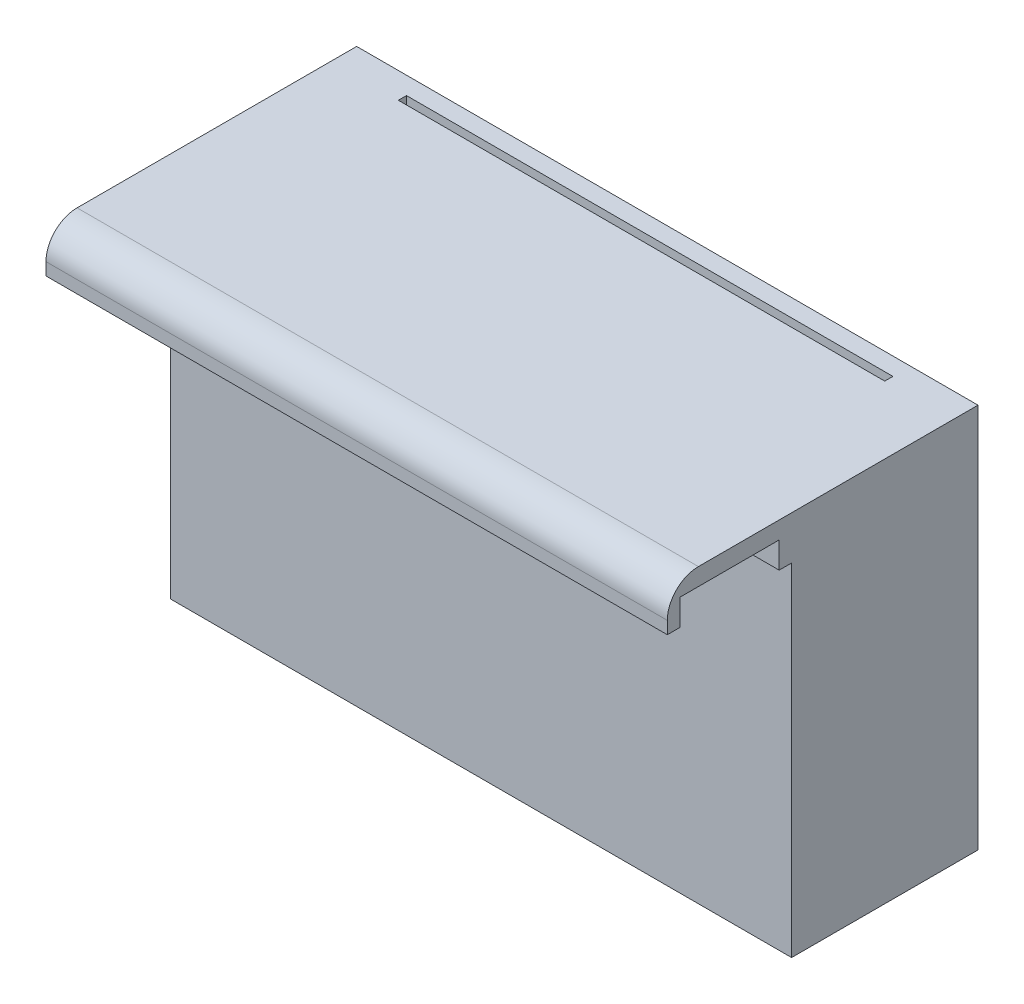
SolidWorks part; units mm, degrees
ref_plane "Front Plane" through (0, 0, 0) normal (0, 0, 1) x (1, 0, 0)
ref_plane "Top Plane" through (0, 0, 0) normal (0, 1, 0) x (1, 0, 0)
ref_plane "Right Plane" through (0, 0, 0) normal (1, 0, 0) x (0, 0, -1)
sketch "Sketch1" plane through (0, 0, 0) normal (0, 1, 0) x (1, 0, 0)
  line L1 (0, 0) -> (-100, 0)
  line L2 (0, 0) -> (0, 20)
  line L3 (0, 20) -> (-100, 20)
  line L4 (-100, 0) -> (-100, 20)
  dimension "D1" = 20
  dimension "D2" = 100
extrude "Boss-Extrude1" add sketch "Sketch1" along normal blind 7
sketch "Sketch2" plane through (-100, 0, 0) normal (-1, 0, 0) x (0, 0, 1)
  line L5 (-20, 0) -> (0, 0) construction
  line L6 (-2, -4.2141) -> (-18, -4.2141)
  line L7 (-2, -4.2141) -> (-2, 4.2141)
  line L8 (-2, 4.2141) -> (-18, 4.2141)
  line L9 (-18, -4.2141) -> (-18, 4.2141)
  line L10 (-2, -4.2141) -> (-18, 4.2141) construction
  line L11 (-2, 4.2141) -> (-18, -4.2141) construction
  point P0 (-10, 0)
  dimension "D1" = 16
extrude "Cut-Extrude1" cut sketch "Sketch2" against normal through all
sketch "Sketch3" plane through (0, 0, -20) normal (0, 0, -1) x (-1, 0, 0)
  line L0 (100, 7) -> (100, 0) construction
  line L1 (0, 7) -> (100, 7)
  line L2 (0, 7) -> (0, -55)
  line L3 (0, -55) -> (100, -55)
  line L4 (100, 7) -> (100, -55)
  dimension "D1" = 62
extrude "Boss-Extrude2" add sketch "Sketch3" along normal blind 30
sketch "Sketch4" plane through (0, 0, -50) normal (0, 0, -1) x (-1, 0, 0)
  line L0 (0, -24) -> (100, -24) construction
  line L1 (0, 7) -> (0, -55) construction
  line L2 (100, -55) -> (100, 7) construction
  line L3 (50, 7) -> (50, -24) construction
  line L4 (100, 7) -> (0, 7) construction
  line L6 (6, -52.25) -> (94, -52.25)
  line L7 (6, -52.25) -> (6, 4.25)
  line L8 (6, 4.25) -> (94, 4.25)
  line L9 (94, -52.25) -> (94, 4.25)
  line L10 (6, -52.25) -> (94, 4.25) construction
  line L11 (6, 4.25) -> (94, -52.25) construction
  dimension "D1" = 88
  dimension "D2" = 56.5
extrude "Cut-Extrude2" cut sketch "Sketch4" against normal blind 27.5
sketch "Sketch5" plane through (-94, 0, 0) normal (1, 0, 0) x (0, 0, -1)
  line L1 (22.5, -27.6063) -> (31.2, -27.6063) construction
  line L2 (22.5, -52.25) -> (22.5, 4.25) construction
  line L3 (38.8863, 2.25) -> (38.8863, 4.25) construction
  line L6 (31.2, 2.25) -> (38.8863, 2.25)
  line L10 (31.2, -50.25) -> (38.8863, -50.25)
  line L12 (22.5, 4.25) -> (50, 4.25) construction
  line L13 (38.8863, -50.25) -> (38.8863, -52.25) construction
  line L14 (22.5, -52.25) -> (50, -52.25) construction
  line L15 (31.2, 2.25) -> (31.2, -50.25)
  line L16 (38.8863, 2.25) -> (38.8863, -50.25)
  dimension "D1" = 8.7
  dimension "D2" = 52.5
extrude "Cut-Extrude3" cut sketch "Sketch5" against normal through all
sketch "Sketch6" plane through (-6, 0, 0) normal (-1, 0, 0) x (0, 0, 1)
  line L0 (-22.5, -24) -> (-50, -24) construction
  line L1 (-22.5, 4.25) -> (-22.5, -52.25) construction
  line L2 (-50, 4.25) -> (-50, -52.25) construction
  line L4 (-50, -17.5) -> (-22.5, -17.5)
  line L5 (-50, -17.5) -> (-50, -30.5)
  line L6 (-50, -30.5) -> (-22.5, -30.5)
  line L7 (-22.5, -17.5) -> (-22.5, -30.5)
  line L8 (-50, -17.5) -> (-22.5, -30.5) construction
  line L9 (-50, -30.5) -> (-22.5, -17.5) construction
  point P6 (-36.25, -24)
  point P11 (-44.5908, -17.5)
  point P12 (-22.5, -17.5)
  dimension "D1" = 13
extrude "Cut-Extrude4" cut sketch "Sketch6" against normal blind 3
sketch "Sketch7" plane through (0, 0, -50) normal (0, 0, -1) x (-1, 0, 0)
  line L0 (6, -52.25) -> (11, -52.25) construction
  line L1 (6, -52.25) -> (94, -52.25) construction
  line L2 (6, -52.25) -> (64, -52.25) construction
  line L3 (6, -52.25) -> (94, -52.25) construction
  line L5 (6, -52.25) -> (64, -52.25)
  line L6 (6, -52.25) -> (6, -54.55)
  line L7 (6, -54.55) -> (64, -54.55)
  line L8 (64, -52.25) -> (64, -54.55)
  dimension "D1" = 5
  dimension "D2" = 58
  dimension "D3" = 2.3
extrude "Cut-Extrude5" cut sketch "Sketch7" against normal blind 23
sketch "Sketch9" plane through (0, -52.25, 0) normal (0, 1, 0) x (1, 0, 0)
  line L0 (-37.9606, 22.5) -> (-37.9606, 38.5) construction
  line L1 (-6, 22.5) -> (-94, 22.5) construction
  line L2 (-64, 27) -> (-64, 50) construction
  line L3 (-37.9606, 38.5) -> (-64, 38.5)
  line L5 (-37.9606, 33.5) -> (-64, 33.5)
  line L6 (-64, 38.5) -> (-64, 33.5)
  line L8 (-37.9606, 38.5) -> (-6.413, 38.5)
  line L10 (-37.9606, 33.5) -> (-6.413, 33.5)
  line L11 (-6.413, 38.5) -> (-6.413, 33.5)
  dimension "D1" = 16
  dimension "D2" = 5
extrude "Cut-Extrude6" cut sketch "Sketch9" against normal blind 23
sketch "Sketch10" plane through (0, 7, 0) normal (0, 1, 0) x (1, 0, 0)
  line L0 (-100, 47.1586) -> (-89.1444, 47.1586) construction
  line L1 (-100, 50) -> (-100, 0) construction
  line L2 (0, 47.1586) -> (-10.8556, 47.1586) construction
  line L3 (0, 0) -> (0, 50) construction
  line L5 (-89.1444, 47.1586) -> (-10.8556, 47.1586)
  line L6 (-89.1444, 47.1586) -> (-89.1444, 45.847)
  line L7 (-89.1444, 45.847) -> (-10.8556, 45.847)
  line L8 (-10.8556, 47.1586) -> (-10.8556, 45.847)
extrude "Cut-Extrude7" cut sketch "Sketch10" against normal blind 2
ref_plane "Plane1" through (0, -24, 0) normal (0, 1, 0) x (1, 0, 0)
mirror "Mirror1" about plane through (0, -24, 0) normal (0, 1, 0) of "Cut-Extrude7"
fillet "Fillet2" radius 5 1 edges at (-50, 7, 0)
